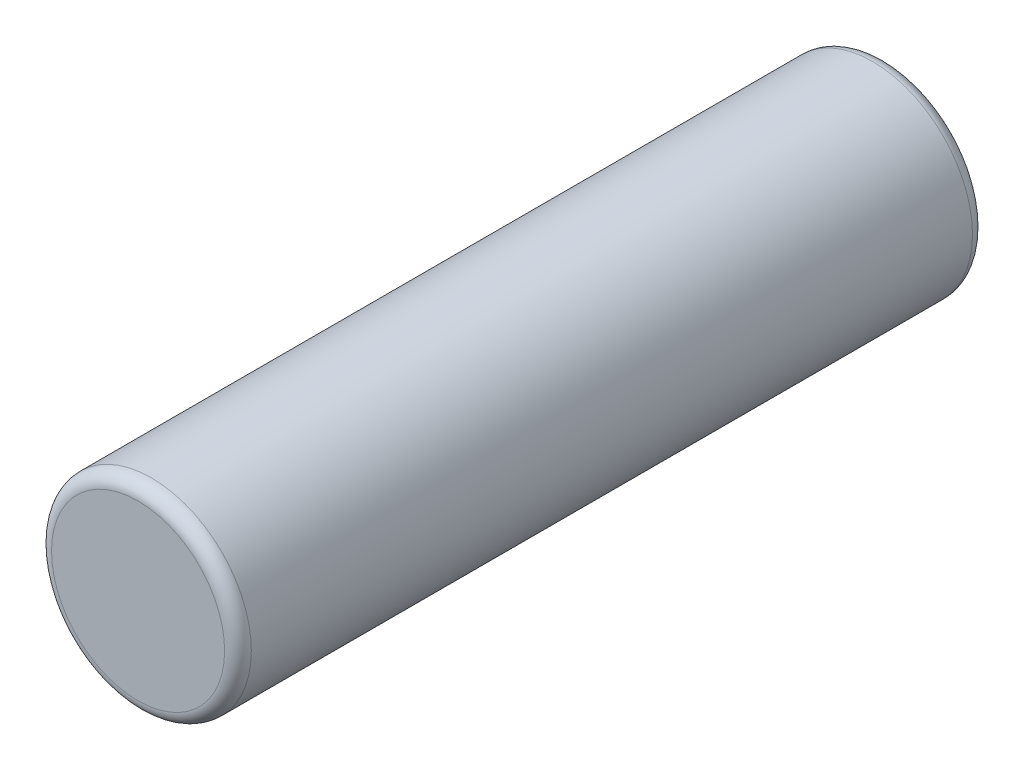
SolidWorks part; units mm, degrees
ref_plane "Front Plane" through (0, 0, 0) normal (0, 0, 1) x (1, 0, 0)
ref_plane "Top Plane" through (0, 0, 0) normal (0, 1, 0) x (1, 0, 0)
ref_plane "Right Plane" through (0, 0, 0) normal (1, 0, 0) x (0, 0, -1)
sketch "Sketch1" plane through (0, 0, 0) normal (0, 0, 1) x (1, 0, 0)
  circle A0 centre (0, 0) radius 47.498
  dimension "D1" = 94.996
extrude "Boss-Extrude1" add sketch "Sketch1" against normal blind 355.6
fillet "Fillet1" radius 6.35 2 edges at (47.498, 0, -355.6) (47.498, 0, 0)
